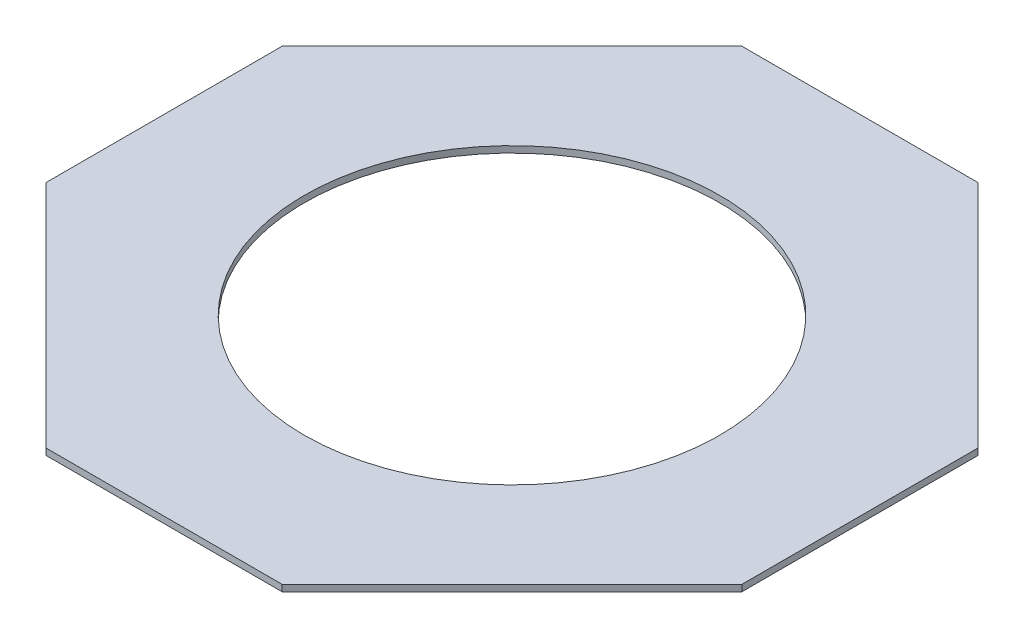
SolidWorks part; units mm, degrees
ref_plane "Front Plane" through (0, 0, 0) normal (0, 0, 1) x (1, 0, 0)
ref_plane "Top Plane" through (0, 0, 0) normal (0, 1, 0) x (1, 0, 0)
ref_plane "Right Plane" through (0, 0, 0) normal (1, 0, 0) x (0, 0, -1)
sketch "Sketch1" plane through (0, 0, 0) normal (0, 1, 0) x (1, 0, 0)
  line L0 (0, 0) -> (0, 70) construction
  line L1 (23.75, 70) -> (-23.75, 70)
  line L2 (0, 0) -> (-70, 0) construction
  line L3 (-70, -23.75) -> (-70, 23.75)
  line L4 (-70, 23.75) -> (-23.75, 70)
  line L5 (-70, -23.75) -> (-23.75, -70)
  line L6 (23.75, -70) -> (-23.75, -70)
  line L7 (70, -23.75) -> (23.75, -70)
  line L8 (70, -23.75) -> (70, 23.75)
  line L9 (70, 23.75) -> (23.75, 70)
  circle A0 centre (0, 0) radius 41.8
  point P10 (0, -70)
  dimension "D5" = 83.6
  dimension "D1" = 70
  dimension "D2" = 23.75
  dimension "D3" = 70
  dimension "D4" = 23.75
extrude "Boss-Extrude2" add sketch "Sketch1" along normal blind 1.3 contours L6 L5 L3 L4 L1 L9 L8 L7 | A0
